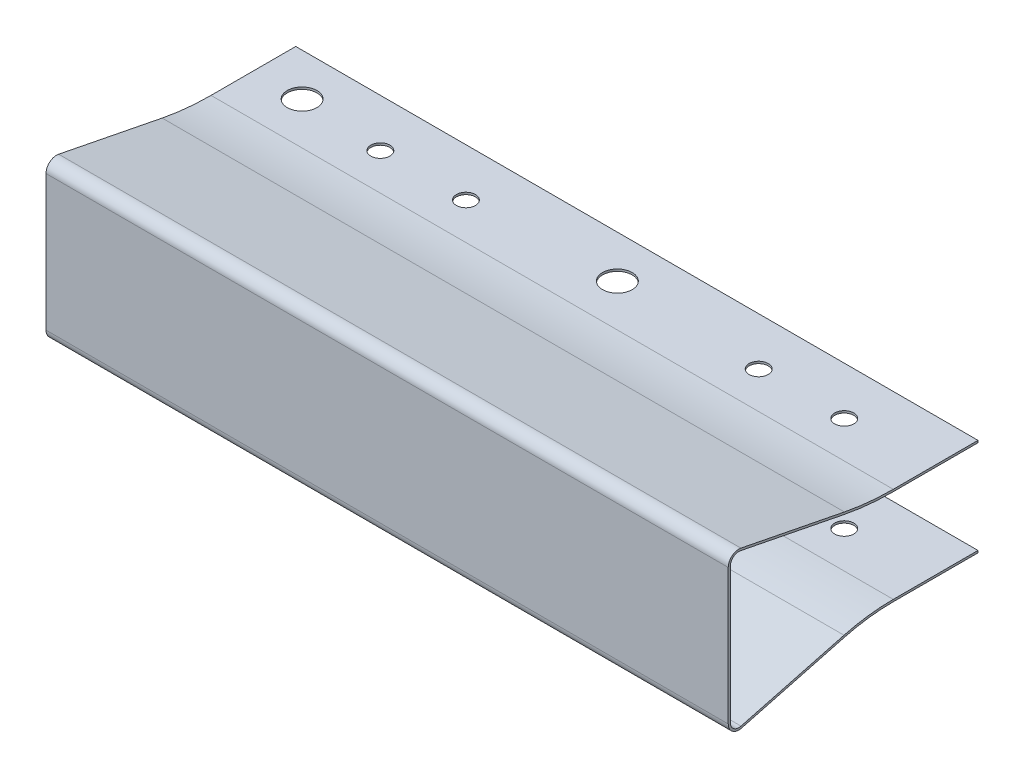
SolidWorks part; units mm, degrees
ref_plane "Front Plane" through (0, 0, 0) normal (0, 0, 1) x (1, 0, 0)
ref_plane "Top Plane" through (0, 0, 0) normal (0, 1, 0) x (1, 0, 0)
ref_plane "Right Plane" through (0, 0, 0) normal (1, 0, 0) x (0, 0, -1)
sketch "Sketch1" plane through (0, 0, 0) normal (1, 0, 0) x (0, 0, -1)
  line L0 (-14.22, 5) -> (-22.22, 5) construction
  line L1 (-24.22, 8) -> (-22.22, 8) construction
  line L2 (-24.22, 8) -> (-24.22, -8) construction
  line L3 (-24.22, -8) -> (-22.22, -8) construction
  line L4 (-14.22, 5) -> (-14.22, 3) construction
  line L5 (-24.22, 8) -> (-14.22, -5) construction
  line L6 (-24.22, -8) -> (-14.22, 5) construction
  line L7 (-22.22, 5) -> (-22.22, 8) construction
  line L8 (-14.22, 3) -> (-21.22, 3) construction
  line L9 (-21.22, 3) -> (-21.22, -3) construction
  line L10 (-21.22, -3) -> (-14.22, -3) construction
  line L11 (-14.22, -5) -> (-22.22, -5) construction
  line L12 (-22.22, -5) -> (-22.22, -8) construction
  line L13 (-14.22, -3) -> (-14.22, -5) construction
  line L14 (-24.22, 8) -> (-24.22, -8)
  line L15 (-10.8136, 6.5687) -> (-23.0262, 8.981)
  line L16 (-5, 5) -> (-5, -5) construction
  line L17 (-5, -5) -> (5, -5) construction
  line L18 (5, 5) -> (5, -5) construction
  line L19 (-5, 5) -> (5, -5) construction
  line L20 (-5, -5) -> (5, 5) construction
  line L21 (-5, 5) -> (5, 5) construction
  line L22 (-5, 5) -> (-5, 6) construction
  line L23 (-5, 6) -> (5, 6) construction
  line L24 (5, 5) -> (5, 6) construction
  line L25 (-10.8136, -5.7553) -> (-22.9645, -8.9668)
  line L26 (-5, -5) -> (5, -5)
  line L27 (-5, 6.25) -> (5, 6.25)
  line L28 (-5, 6) -> (5, 6)
  line L29 (-10.7651, 6.8139) -> (-22.9778, 9.2263)
  line L30 (-24.47, 8) -> (-24.47, -8)
  line L31 (-10.7497, -5.997) -> (-22.9006, -9.2085)
  line L32 (-5, -5.25) -> (5, -5.25)
  line L33 (5, 6.25) -> (5, 6)
  line L34 (5, -5) -> (5, -5.25)
  arc A0 (-24.22, -8) -> (-22.9645, -8.9668) centre (-23.22, -8) ccw
  arc A1 (-23.0262, 8.981) -> (-24.22, 8) centre (-23.22, 8) ccw
  arc A2 (-5, 6.25) -> (-10.7651, 6.8139) centre (-5, 36) cw
  arc A3 (-22.9778, 9.2263) -> (-24.47, 8) centre (-23.22, 8) ccw
  arc A4 (-24.47, -8) -> (-22.9006, -9.2085) centre (-23.22, -8) ccw
  arc A5 (-5, -5.25) -> (-10.7497, -5.997) centre (-5, -27.7512) ccw
  arc A6 (-5, -5) -> (-10.8136, -5.7553) centre (-5, -27.7512) ccw
  arc A7 (-5, 6) -> (-10.8136, 6.5687) centre (-5, 36) cw
  point P0 (-18.0662, 0)
  point P1 (0, 0)
  dimension "D13" = 30
  dimension "D17" = 1
  dimension "D1" = 16
  dimension "D2" = 10
  dimension "D3" = 2
  dimension "D4" = 2
  dimension "D5" = 2
  dimension "D6" = 3
  dimension "D7" = 6
  dimension "D8" = 3
  dimension "D9" = 10
  dimension "D10" = 10
  dimension "D11" = 16.22
  dimension "D12" = 1
  dimension "D14" = 0.25
extrude "Extrude1" add sketch "Sketch1" along normal mid plane 80.5
sketch "Sketch2" plane through (0, 0, 0) normal (0, 1, 0) x (1, 0, 0)
  line L0 (40.25, 5) -> (-40.25, 5) construction
  line L1 (-40.25, 5) -> (-40.25, -5) construction
  circle A0 centre (-34.5, 0) radius 1.75
  circle A1 centre (-24.62, -0.65) radius 1.125
  circle A2 centre (-14.52, -0.65) radius 1.125
  circle A3 centre (2.7, 0) radius 1.75
  circle A4 centre (20.02, -0.65) radius 1.125
  circle A5 centre (30.12, -0.65) radius 1.125
  dimension "D1" = 3.5
  dimension "D2" = 3.5
  dimension "D3" = 2.25
  dimension "D4" = 2.25
  dimension "D5" = 2.25
  dimension "D6" = 2.25
  dimension "D7" = 5
  dimension "D8" = 5.75
  dimension "D9" = 10.1
  dimension "D10" = 10.1
  dimension "D11" = 37.2
  dimension "D12" = 0.65
  dimension "D13" = 9.88
  dimension "D14" = 17.32
extrude "Cut-Extrude1" cut sketch "Sketch2" against normal through all and the other way through all
